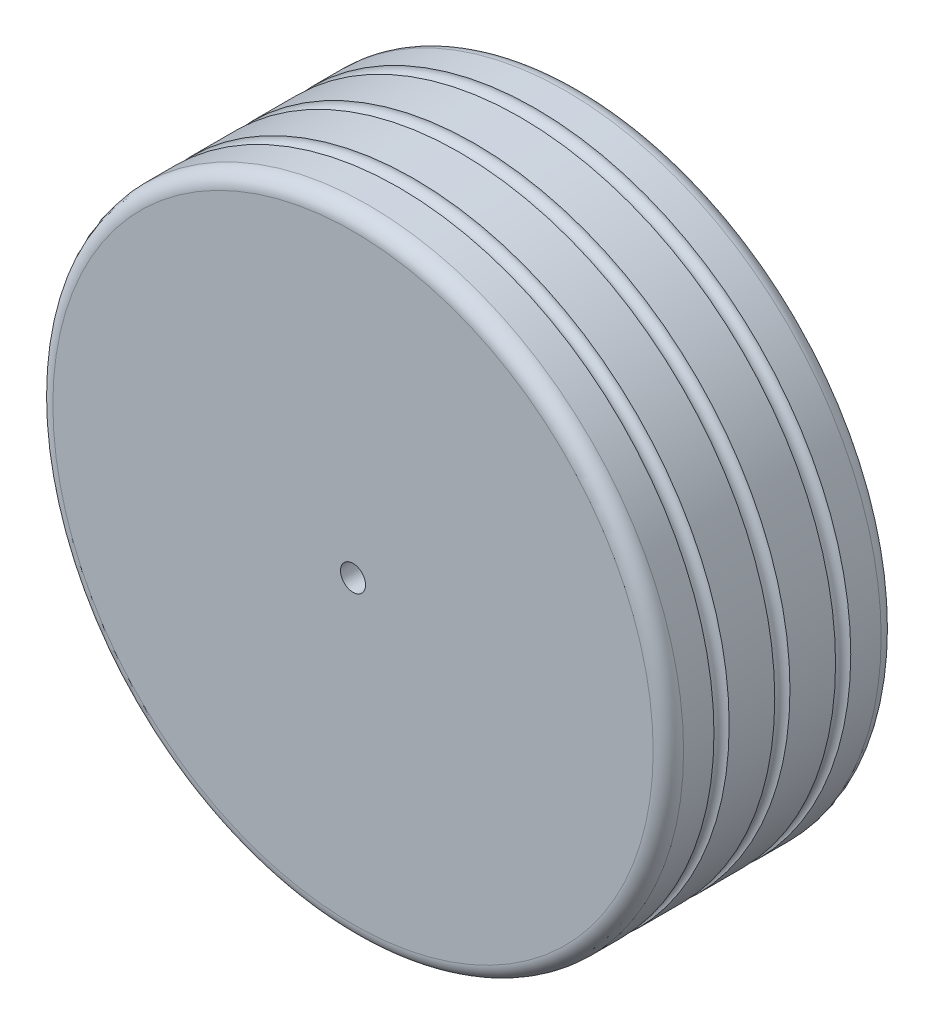
SolidWorks part; units mm, degrees
ref_plane "Přední rovina" through (0, 0, 0) normal (0, 0, 1) x (1, 0, 0)
ref_plane "Horní rovina" through (0, 0, 0) normal (0, 1, 0) x (1, 0, 0)
ref_plane "Pravá rovina" through (0, 0, 0) normal (1, 0, 0) x (0, 0, -1)
sketch "Skica1" plane through (0, 0, 0) normal (0, 0, 1) x (1, 0, 0)
  circle A0 centre (0, 0) radius 41.5
  dimension "D1" = 83
extrude "Přidat vysunutím1" add sketch "Skica1" along normal blind 30
fillet "Zaoblit1" radius 2 2 edges at (41.5, 0, 0) (41.5, 0, 30)
sketch "Skica2" plane through (0, 0, 30) normal (0, 0, 1) x (1, 0, 0)
  circle A0 centre (0, 0) radius 1.65
  dimension "D1" = 3.3
extrude "Odebrat vysunutím1" cut sketch "Skica2" against normal blind 7
sketch "Skica3" plane through (0, 0, 0) normal (0, 0, -1) x (-1, 0, 0)
  circle A0 centre (0, 0) radius 25
  dimension "D1" = 50
extrude "Odebrat vysunutím2" cut sketch "Skica3" against normal blind 10
fillet "Zaoblit2" radius 3 2 edges at (-25, 0, 0) (-25, 0, 10)
sketch "Skica4" plane through (0, 0, 0) normal (1, 0, 0) x (0, 0, -1)
  line L0 (-2, 41.5) -> (-28, 41.5) construction
  line L1 (0, -39.5) -> (0, 39.5) construction
  line L2 (-30, 39.5) -> (-30, -39.5) construction
  circle A0 centre (-7, 41.5) radius 1
  circle A1 centre (-15, 41.5) radius 1
  circle A2 centre (-23, 41.5) radius 1
  dimension "D1" = 2
  dimension "D2" = 2
  dimension "D3" = 2
  dimension "D4" = 7
  dimension "D5" = 7
  dimension "D6" = 15
  dimension "D7" = 41.5
  dimension "D8" = 41.5
revolve "Odebrat rotací1" cut sketch "Skica4" angle 360 about axis through (0, 0, 23) along (0, 0, 1)
